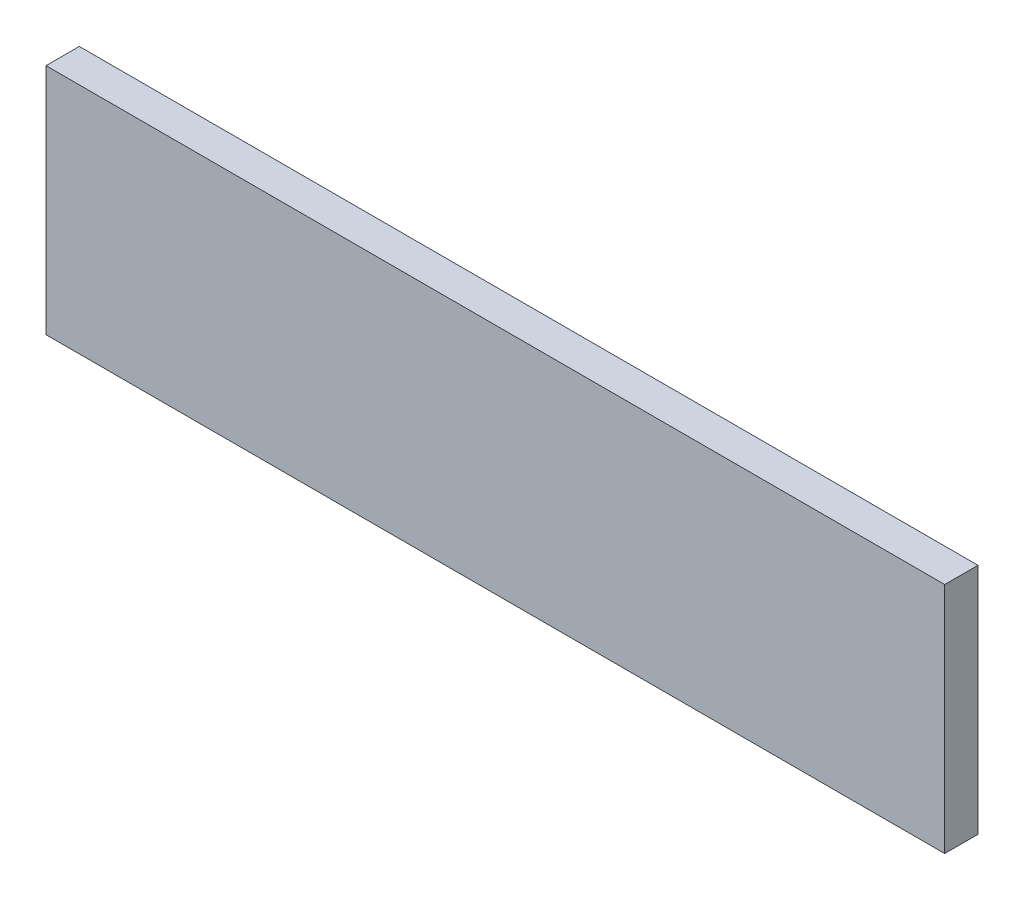
SolidWorks part; units mm, degrees
ref_plane "Front Plane" through (0, 0, 0) normal (0, 0, 1) x (1, 0, 0)
ref_plane "Top Plane" through (0, 0, 0) normal (0, 1, 0) x (1, 0, 0)
ref_plane "Right Plane" through (0, 0, 0) normal (1, 0, 0) x (0, 0, -1)
sketch "Sketch2" plane through (0, 0, 0) normal (0, 0, 1) x (1, 0, 0)
  line L1 (0, 0) -> (500, 0)
  line L2 (0, 0) -> (0, 50)
  line L3 (0, 50) -> (500, 50)
  line L4 (500, 0) -> (500, 50)
  dimension "D1" = 500
  dimension "D2" = 50
extrude "Boss-Extrude1" add sketch "Sketch2" along normal blind 10
sketch "Sketch3" plane through (0, 0, 0) normal (0, 0, -1) x (-1, 0, 0)
  line L0 (0, 0) -> (-500, 0) construction
  line L1 (0, 60) -> (-200, 60)
  line L2 (0, 60) -> (0, 0)
  line L3 (0, 0) -> (-200, 0)
  line L4 (-200, 60) -> (-200, 0)
  line L5 (0, 50) -> (0, 0) construction
  line L7 (-500, 50) -> (-470, 50)
  line L8 (-500, 50) -> (-500, 0)
  line L9 (-500, 0) -> (-470, 0)
  line L10 (-470, 50) -> (-470, 0)
  dimension "D1" = 200
  dimension "D2" = 30
extrude "Cut-Extrude1" cut sketch "Sketch3" against normal up to next
sketch "Sketch4" plane through (0, 50, 0) normal (0, 1, 0) x (1, 0, 0)
  line L1 (470, 0) -> (200, 0)
  line L2 (470, 0) -> (470, -10)
  line L3 (470, -10) -> (200, -10)
  line L4 (200, 0) -> (200, -10)
extrude "Boss-Extrude2" add sketch "Sketch4" along normal blind 20
